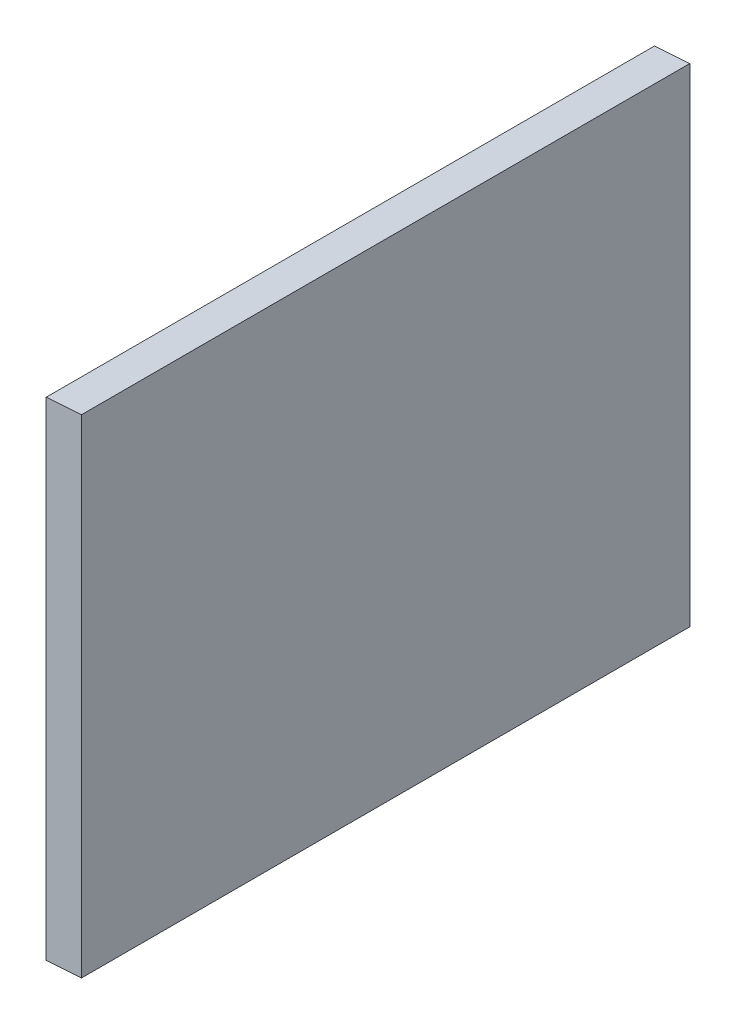
SolidWorks part; units mm, degrees
ref_plane "Front Plane" through (0, 0, 0) normal (0, 0, 1) x (1, 0, 0)
ref_plane "Top Plane" through (0, 0, 0) normal (0, 1, 0) x (1, 0, 0)
ref_plane "Right Plane" through (0, 0, 0) normal (1, 0, 0) x (0, 0, -1)
sketch "Sketch1" plane through (0, 0, 0) normal (0, 0, 1) x (1, 0, 0)
  line L0 (0, 0) -> (0, 320.8)
  line L1 (0, 320.8) -> (-23.2, 319.1777)
  line L2 (-23.2, 319.1777) -> (-23.2, -1.6223)
  line L3 (-23.2, -1.6223) -> (0, 0)
  dimension "D1" = 86
  dimension "D2" = 23.2
  dimension "D3" = 320.8
extrude "Boss-Extrude1" add sketch "Sketch1" along normal blind 400
